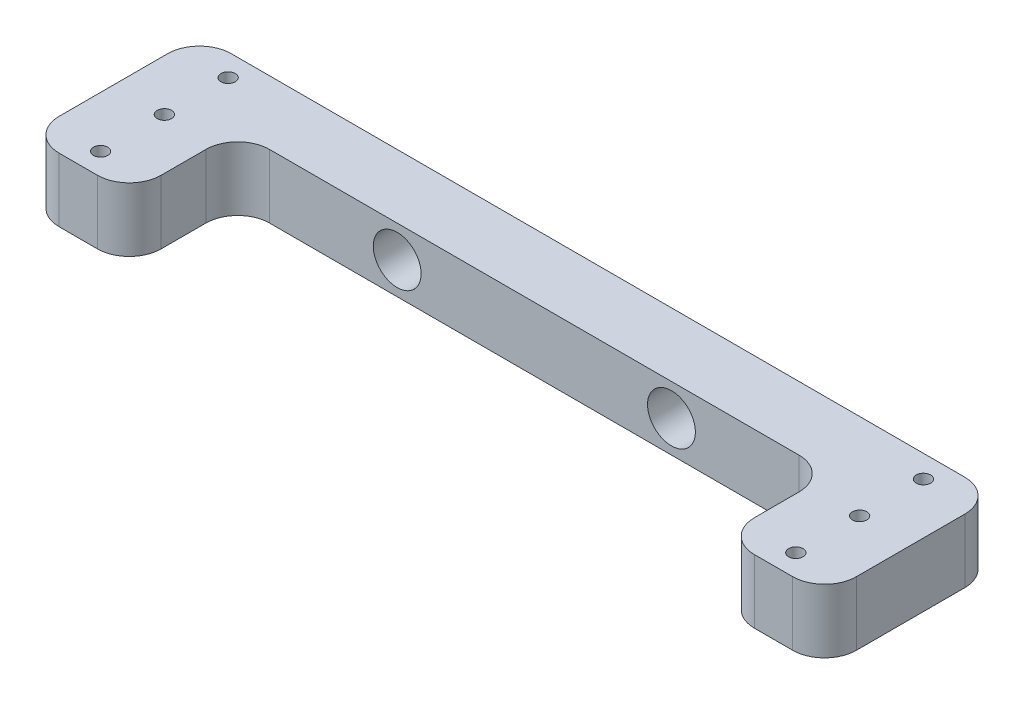
SolidWorks part; units mm, degrees
ref_plane "Front Plane" through (0, 0, 0) normal (0, 0, 1) x (1, 0, 0)
ref_plane "Top Plane" through (0, 0, 0) normal (0, 1, 0) x (1, 0, 0)
ref_plane "Right Plane" through (0, 0, 0) normal (1, 0, 0) x (0, 0, -1)
sketch "Sketch1" plane through (0, 0, 0) normal (0, 1, 0) x (1, 0, 0)
  line L0 (115, 20) -> (-115, 20)
  line L1 (-125, 10) -> (-125, -24)
  line L2 (-115, -34) -> (-103, -34)
  line L3 (-93, -24) -> (-93, -10)
  line L4 (-83, 0) -> (-30, 0)
  line L5 (-20, -10) -> (-20, -60) construction
  line L6 (-10, -70) -> (10, -70) construction
  line L7 (-109, 13) -> (-109, -58.0945) construction
  line L8 (0, 63.2774) -> (0, -87.5311) construction
  line L9 (109, 13) -> (109, -58.0945) construction
  line L10 (20, -10) -> (20, -60) construction
  line L11 (83, 0) -> (30, 0)
  line L12 (93, -24) -> (93, -10)
  line L13 (115, -34) -> (103, -34)
  line L14 (125, 10) -> (125, -24)
  line L15 (-30, 0) -> (30, 0)
  circle A0 centre (-109, 13) radius 2.25
  circle A3 centre (-109, -7) radius 2.25
  circle A4 centre (-109, -27) radius 2.25
  arc A5 (-20, -60) -> (-10, -70) centre (-10, -60) ccw construction
  arc A6 (-103, -34) -> (-93, -24) centre (-103, -24) ccw
  arc A7 (-125, -24) -> (-115, -34) centre (-115, -24) ccw
  arc A8 (-115, 20) -> (-125, 10) centre (-115, 10) ccw
  arc A9 (-30, 0) -> (-20, -10) centre (-30, -10) cw construction
  arc A10 (-93, -10) -> (-83, 0) centre (-83, -10) cw
  arc A11 (93, -10) -> (83, 0) centre (83, -10) ccw
  arc A12 (30, 0) -> (20, -10) centre (30, -10) ccw construction
  arc A13 (115, 20) -> (125, 10) centre (115, 10) cw
  arc A14 (125, -24) -> (115, -34) centre (115, -24) cw
  arc A15 (103, -34) -> (93, -24) centre (103, -24) cw
  arc A16 (20, -60) -> (10, -70) centre (10, -60) cw construction
  circle A17 centre (109, -27) radius 2.25
  circle A18 centre (109, -7) radius 2.25
  circle A19 centre (109, 13) radius 2.25
  point P0 (20, 0)
  point P9 (0, 20)
  point P18 (-20, -70)
  point P23 (-93, -34)
  point P26 (-125, -34)
  point P29 (-125, 20)
  point P32 (-20, 0)
  point P60 (0, -70)
  point P61 (125, 20)
  point P62 (125, -34)
  point P63 (93, -34)
  point P64 (20, -70)
  dimension "D8" = 7
  dimension "D9" = 4.5
  dimension "D10" = 7
  dimension "D11" = 10
  dimension "D12" = 10
  dimension "D1" = 125
  dimension "D2" = 54
  dimension "D3" = 70
  dimension "D4" = 32
  dimension "D5" = 20
  dimension "D6" = 20
  dimension "D7" = 3
extrude "Boss-Extrude1" add sketch "Sketch1" along normal blind 20
sketch "Sketch6" plane through (0, 0, 0) normal (0, 0, 1) x (1, 0, 0)
  line L0 (-125, 20) -> (-125, 0) construction
  line L3 (-43, 10) -> (-64.3541, 10) construction
  line L4 (-83, 20) -> (83, 20) construction
  line L5 (-83, 0) -> (83, 0) construction
  line L6 (0, 30.6807) -> (0, -18.5171) construction
  circle A0 centre (-43, 10) radius 7.5
  circle A1 centre (43, 10) radius 7.5
  dimension "D1" = 15
  dimension "D2" = 82
extrude "Cut-Extrude1" cut sketch "Sketch6" against normal blind 16
sketch "Sketch7" plane through (0, 0, -16) normal (0, 0, 1) x (1, 0, 0)
  line L0 (0, 30.9145) -> (0, -14.6648) construction
  circle A0 centre (-43, 10) radius 2.5
  circle A1 centre (-43, 10) radius 7.5 construction
  circle A2 centre (-43, 10) radius 7.5 construction
  circle A3 centre (43, 10) radius 2.5
  dimension "D1" = 5
extrude "Cut-Extrude2" cut sketch "Sketch7" against normal up to next
